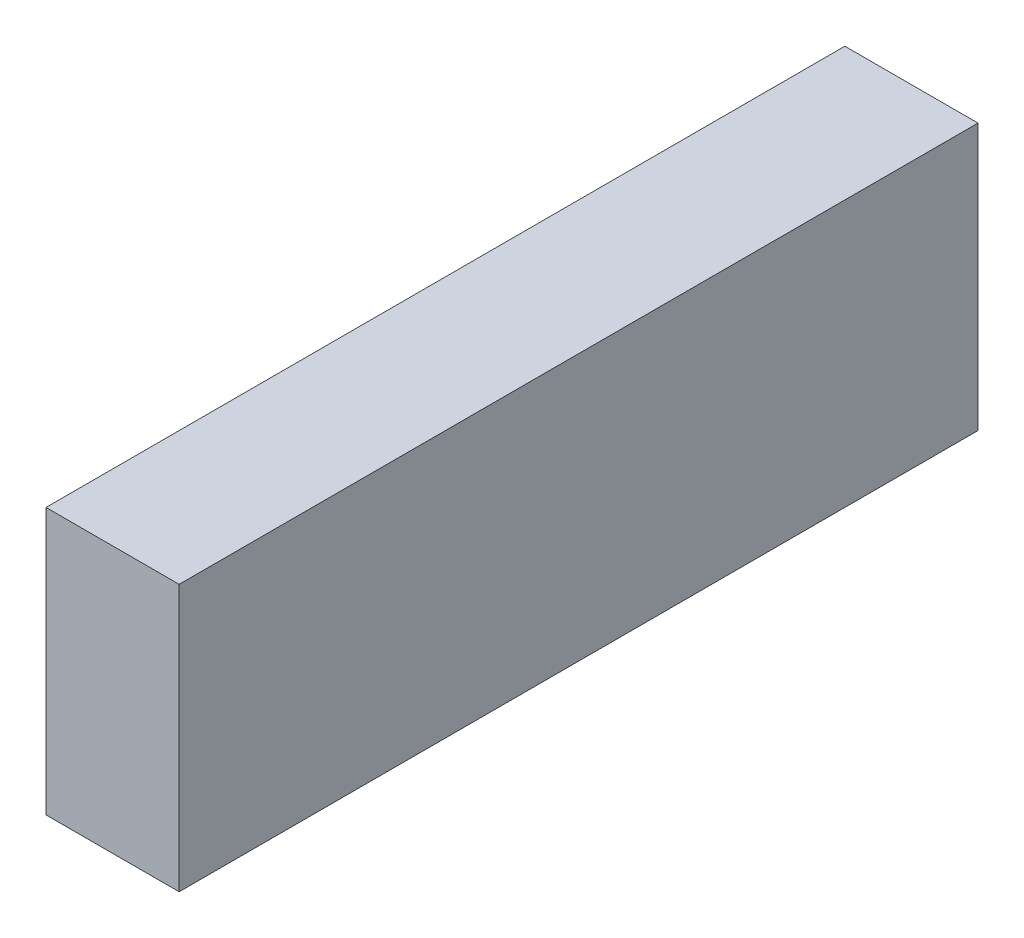
SolidWorks part; units mm, degrees
ref_plane "Plan de face" through (0, 0, 0) normal (0, 0, 1) x (1, 0, 0)
ref_plane "Plan de dessus" through (0, 0, 0) normal (0, 1, 0) x (1, 0, 0)
ref_plane "Plan de droite" through (0, 0, 0) normal (1, 0, 0) x (0, 0, -1)
sketch "Esquisse3" plane through (0, 0, 0) normal (0, 0, 1) x (1, 0, 0)
  line L1 (-79.8395, -22.3426) -> (-74.8395, -22.3426)
  line L2 (-79.8395, -22.3426) -> (-79.8395, -32.3426)
  line L3 (-79.8395, -32.3426) -> (-74.8395, -32.3426)
  line L4 (-74.8395, -22.3426) -> (-74.8395, -32.3426)
  line L5 (-79.8395, -22.3426) -> (-74.8395, -32.3426) construction
  line L6 (-79.8395, -32.3426) -> (-74.8395, -22.3426) construction
  point P0 (-77.3395, -27.3426)
  dimension "D1" = 5
  dimension "D2" = 10
extrude "Boss.-Extru.3" add sketch "Esquisse3" along normal mid plane 30
